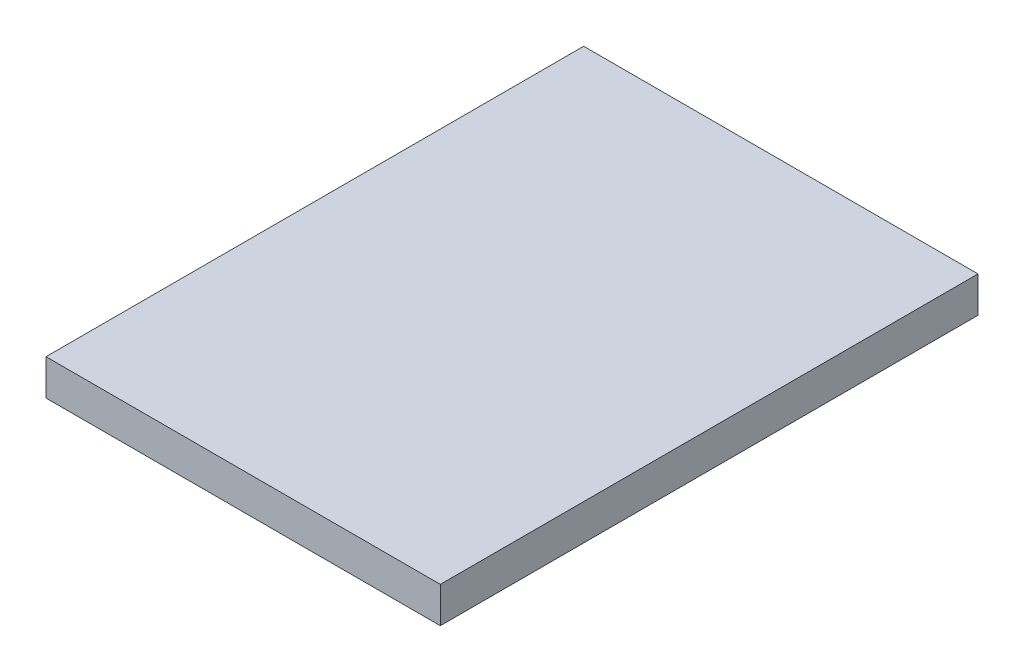
SolidWorks part; units mm, degrees
material "Copper"
ref_plane "Front Plane" through (0, 0, 0) normal (0, 0, 1) x (1, 0, 0)
ref_plane "Top Plane" through (0, 0, 0) normal (0, 1, 0) x (1, 0, 0)
ref_plane "Right Plane" through (0, 0, 0) normal (1, 0, 0) x (0, 0, -1)
sketch "Sketch1" plane through (0, 0, 0) normal (0, 1, 0) x (1, 0, 0)
  line L1 (110, -150) -> (-110, -150)
  line L2 (110, -150) -> (110, 150)
  line L3 (110, 150) -> (-110, 150)
  line L4 (-110, -150) -> (-110, 150)
  line L5 (110, -150) -> (-110, 150) construction
  line L6 (110, 150) -> (-110, -150) construction
  point P0 (0, 0)
  dimension "D1" = 300
  dimension "D2" = 220
extrude "Boss-Extrude1" add sketch "Sketch1" along normal blind 20
